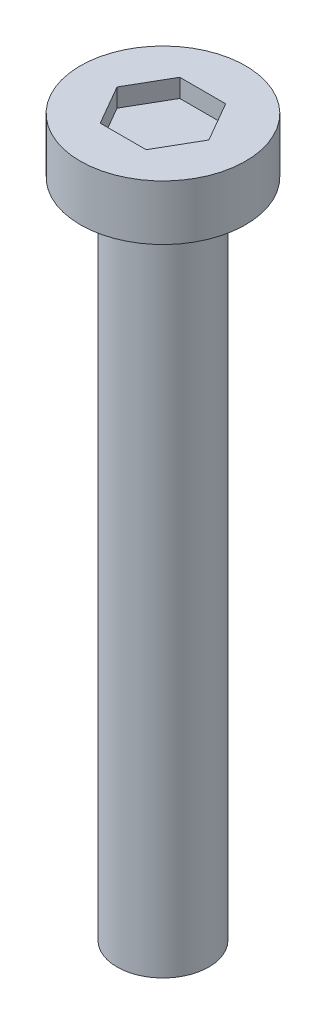
SolidWorks part; units mm, degrees
ref_plane "Front Plane" through (0, 0, 0) normal (0, 0, 1) x (1, 0, 0)
ref_plane "Top Plane" through (0, 0, 0) normal (0, 1, 0) x (1, 0, 0)
ref_plane "Right Plane" through (0, 0, 0) normal (1, 0, 0) x (0, 0, -1)
sketch "Sketch1" plane through (0, 0, 0) normal (0, 1, 0) x (1, 0, 0)
  circle A0 centre (0, 0) radius 1.25
  dimension "D1" = 2.5
extrude "Boss-Extrude1" add sketch "Sketch1" along normal blind 18
sketch "Sketch4" plane through (0, 18, 0) normal (0, 1, 0) x (1, 0, 0)
  circle A0 centre (0, 0) radius 2.25
  dimension "D1" = 4.5
extrude "Boss-Extrude2" add sketch "Sketch4" along normal blind 1.5
sketch "Sketch5" plane through (0, 19.5, 0) normal (0, 1, 0) x (1, 0, 0)
  line L1 (1.25, 0) -> (0.625, 1.0825)
  line L2 (0.625, 1.0825) -> (-0.625, 1.0825)
  line L3 (-0.625, 1.0825) -> (-1.25, 0)
  line L4 (-1.25, 0) -> (-0.625, -1.0825)
  line L5 (-0.625, -1.0825) -> (0.625, -1.0825)
  line L6 (0.625, -1.0825) -> (1.25, 0)
  circle A0 centre (0, 0) radius 1.0825 construction
  dimension "D1" = 1.25
extrude "Cut-Extrude1" cut sketch "Sketch5" against normal blind 0.5
thread "Thread1" pitch 0.7 start angle 0, offset 0, length 16, pitch 0.7, diameter 2.5
ref_plane "Plane1" through (1.25, 0, 0) normal (0, 0, 1) x (1, 0, 0)
sketch "Thread Profile1" plane through (1.25, 0, 0) normal (0, 0, 1) x (1, 0, 0)
  line L0 (0, 0) -> (0, 0.7) construction
  line L1 (0, 0) -> (0.3789, 0.2187)
  line L2 (0.3789, 0.2187) -> (0.3789, 0.3062)
  line L3 (0.3789, 0.3062) -> (0, 0.525)
  line L4 (0.3789, 0.2625) -> (0, 0.2625) construction
  line L11 (0, 0) -> (0, 0.525)
  point P2 (0, 0)
  dimension "Pitch" = 0.7
  dimension "Profile_Angle" = 60
  dimension "Profile_Land" = 0.0875
  dimension "Profile_Height" = 0.3789
